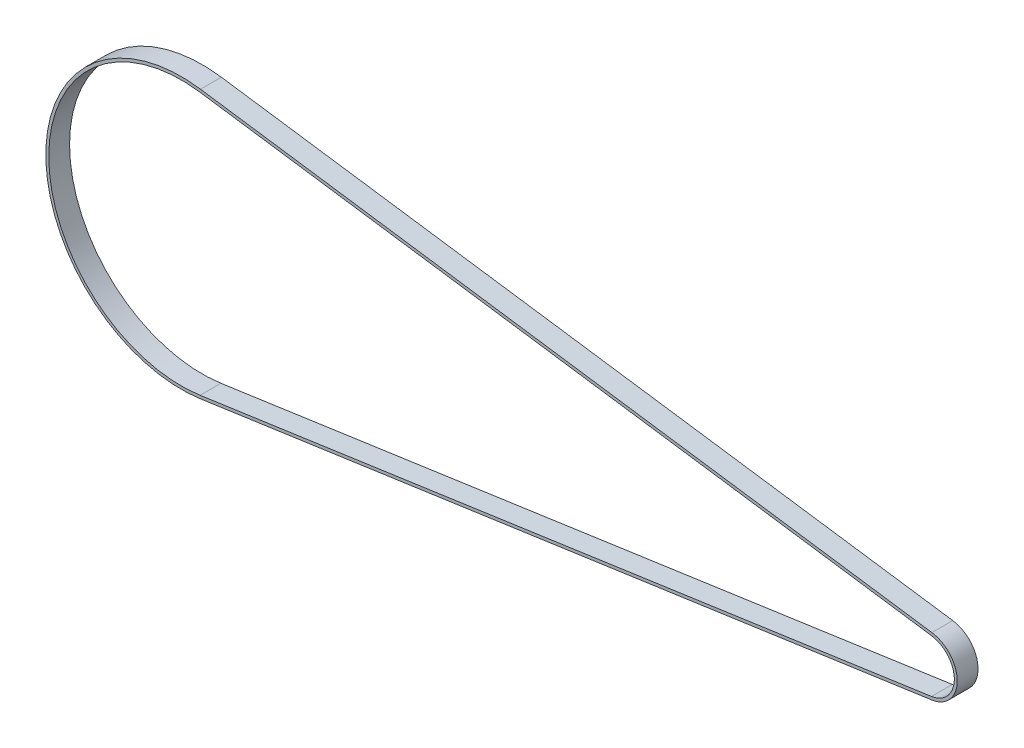
SolidWorks part; units mm, degrees
ref_plane "Front Plane" through (0, 0, 0) normal (0, 0, 1) x (1, 0, 0)
ref_plane "Top Plane" through (0, 0, 0) normal (0, 1, 0) x (1, 0, 0)
ref_plane "Right Plane" through (0, 0, 0) normal (1, 0, 0) x (0, 0, -1)
sketch "Sketch2" plane through (0, 0, 0) normal (0, 0, 1) x (1, 0, 0)
  line L0 (0, 0) -> (1, 0) construction
  line L1 (0, 0) -> (0, 1) construction
  line L2 (2.5778, -17.9771) -> (-497.1471, -89.6342)
  line L3 (-497.1471, 89.6342) -> (2.5778, 17.9771)
  arc A0 (2.5778, 17.9771) -> (2.5778, -17.9771) centre (0, 0) cw
  arc A1 (-497.1471, -89.6342) -> (-497.1471, 89.6342) centre (-510, 0) cw
extrude "Extrude-Thin1" add sketch "Sketch2" against normal blind 14.224 thin thin type one direction wall 2
